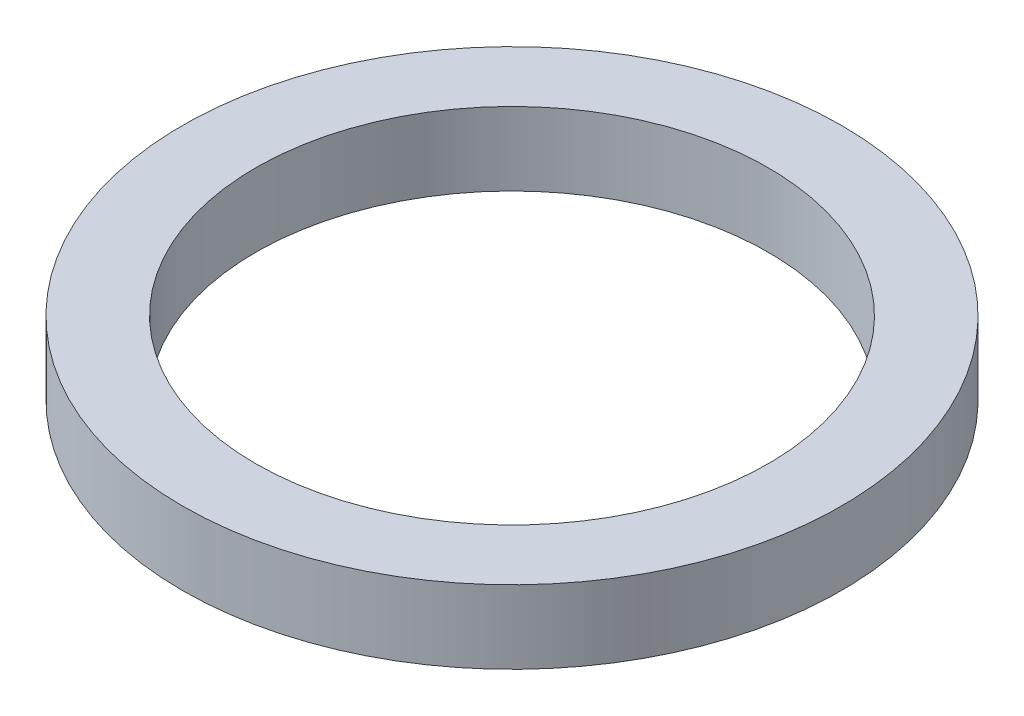
SolidWorks part; units mm, degrees
ref_plane "Front Plane" through (0, 0, 0) normal (0, 0, 1) x (1, 0, 0)
ref_plane "Top Plane" through (0, 0, 0) normal (0, 1, 0) x (1, 0, 0)
ref_plane "Right Plane" through (0, 0, 0) normal (1, 0, 0) x (0, 0, -1)
sketch "Sketch2" plane through (0, 0, 0) normal (0, 1, 0) x (1, 0, 0)
  circle A0 centre (0, 0) radius 9
extrude "Boss-Extrude1" add sketch "Sketch2" along normal blind 2
sketch "Sketch4" plane through (0, 2, 0) normal (0, 1, 0) x (1, 0, 0)
  circle A0 centre (0, 0) radius 7
extrude "Cut-Extrude3" cut sketch "Sketch4" against normal blind 2
